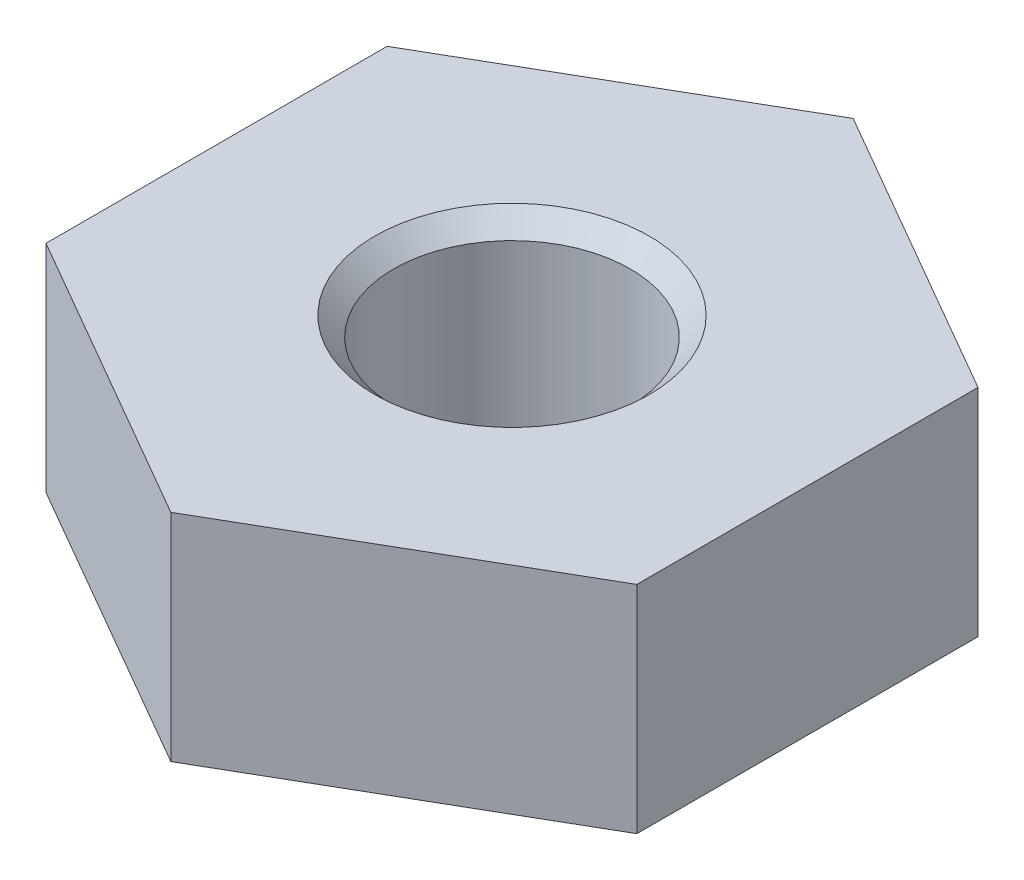
SolidWorks part; units mm, degrees
material "Titanium Ti-8Mn, Annealed"
ref_plane "Front Plane" through (0, 0, 0) normal (0, 0, 1) x (1, 0, 0)
ref_plane "Top Plane" through (0, 0, 0) normal (0, 1, 0) x (1, 0, 0)
ref_plane "Right Plane" through (0, 0, 0) normal (1, 0, 0) x (0, 0, -1)
sketch "Sketch1" plane through (0, 0, 0) normal (0, 1, 0) x (1, 0, 0)
  line L1 (0, -4.5754) -> (3.9624, -2.2877)
  line L2 (3.9624, -2.2877) -> (3.9624, 2.2877)
  line L3 (3.9624, 2.2877) -> (0, 4.5754)
  line L4 (0, 4.5754) -> (-3.9624, 2.2877)
  line L5 (-3.9624, 2.2877) -> (-3.9624, -2.2877)
  line L6 (-3.9624, -2.2877) -> (0, -4.5754)
  circle A0 centre (0, 0) radius 3.9624 construction
  point P1 (-3.9624, 0)
  point P10 (3.9624, 0)
  dimension "D1" = 7.9248
extrude "Boss-Extrude1" add sketch "Sketch1" along normal blind 2.8956
sketch "Sketch2" plane through (0, 2.8956, 0) normal (0, 1, 0) x (1, 0, 0)
  circle A0 centre (0, 0) radius 1.5875
  dimension "D1" = 3.175
extrude "Cut-Extrude1" cut sketch "Sketch2" against normal blind 2.8956
chamfer "Chamfer3" distance 0.254 angle 45 1 edges at (0, 2.8956, 1.5875)
chamfer "Chamfer4" distance 0.254 angle 45 1 edges at (0, 0, 1.5875)
